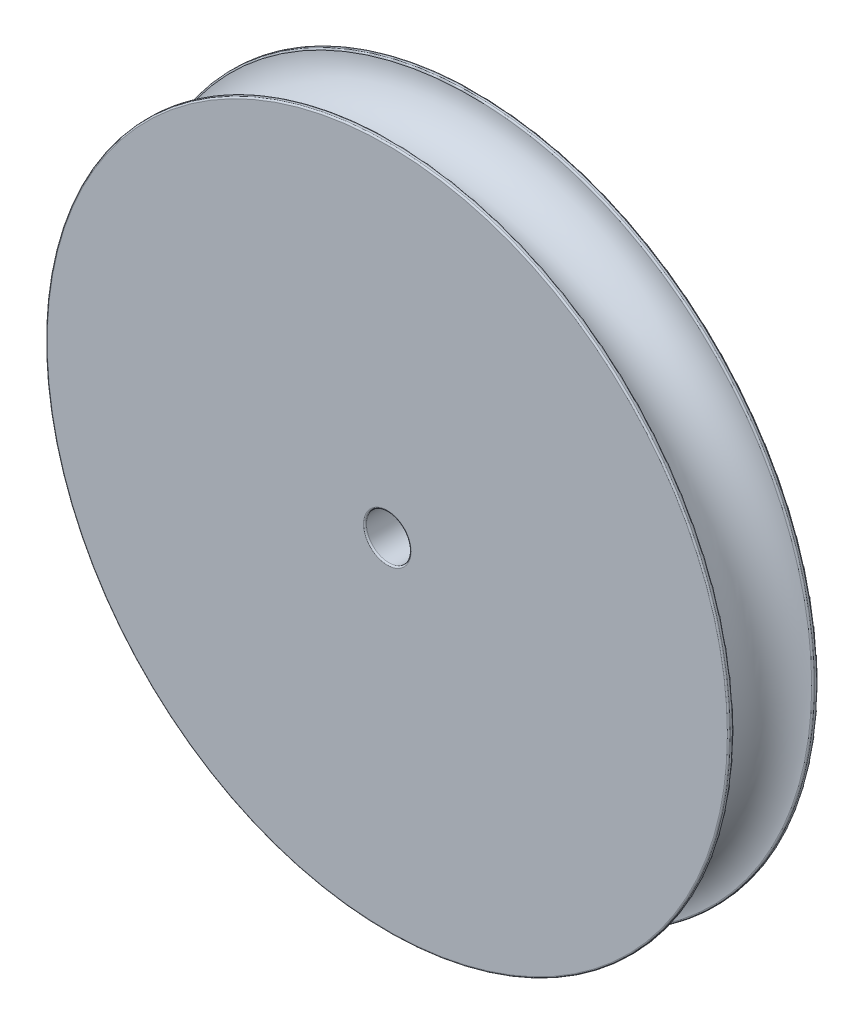
SolidWorks part; units mm, degrees
material "ABS"
ref_plane "Face" through (0, 0, 0) normal (0, 0, 1) x (1, 0, 0)
ref_plane "Dessus" through (0, 0, 0) normal (0, 1, 0) x (1, 0, 0)
ref_plane "Droite" through (0, 0, 0) normal (1, 0, 0) x (0, 0, -1)
sketch "Esquisse1" plane through (0, 0, 0) normal (0, 0, 1) x (1, 0, 0)
  circle A0 centre (0, 0) radius 22.98
  dimension "D1" = 45.96
extrude "Boss.-Extru.2" add sketch "Esquisse1" along normal mid plane 6
ref_axis "Axe1" through (0, 0, 3) along (0, 0, -1)
sketch "Esquisse6" plane through (0, 0, 0) normal (0, 1, 0) x (1, 0, 0)
  line L0 (-22.98, 3) -> (-22.98, -3) construction
  circle A0 centre (-22.98, 0) radius 2.67
  dimension "D1" = 5.34
revolve "Enlèvement de matière-Révolution1" cut sketch "Esquisse6" angle 360 about axis through (0, 0, 3) along (0, 0, -1)
sketch "Esquisse7" plane through (0, 0, 0) normal (0, 0, 1) x (1, 0, 0)
  circle A0 centre (0, 0) radius 6.5
  dimension "D1" = 13
extrude "Boss.-Extru.3" add sketch "Esquisse7" against normal blind 13
sketch "Esquisse8" plane through (0, 0, 0) normal (0, 0, 1) x (1, 0, 0)
  circle A0 centre (0, 0) radius 1.5
  dimension "D1" = 3
extrude "Enlèv. mat.-Extru.1" cut sketch "Esquisse8" against normal mid plane 30
sketch "Esquisse10" plane through (0, 0, 0) normal (1, 0, 0) x (0, 0, -1)
  circle A0 centre (8.5, 0) radius 1.5
  dimension "D2" = 3
extrude "Enlèv. mat.-Extru.2" cut sketch "Esquisse10" against normal blind 10
fillet "Congé1" radius 1 1 edges at (6.5, 0, -13)
fillet "Congé2" radius 1 1 edges at (6.5, 0, -3)
fillet "Congé3" radius 0.1 1 edges at (22.98, 0, -3)
fillet "Congé4" radius 0.1 1 edges at (22.98, 0, -2.67)
fillet "Congé5" radius 0.1 1 edges at (-22.98, 0, 2.67)
fillet "Congé6" radius 0.1 1 edges at (22.98, 0, 3)
fillet "Congé7" radius 0.1 1 edges at (1.5, 0, 3)
fillet "Congé8" radius 0.1 1 edges at (1.5, 0, -13)
fillet "Congé9" radius 0.1 1 edges at (-6.493, 0.3008, -7.0305)
